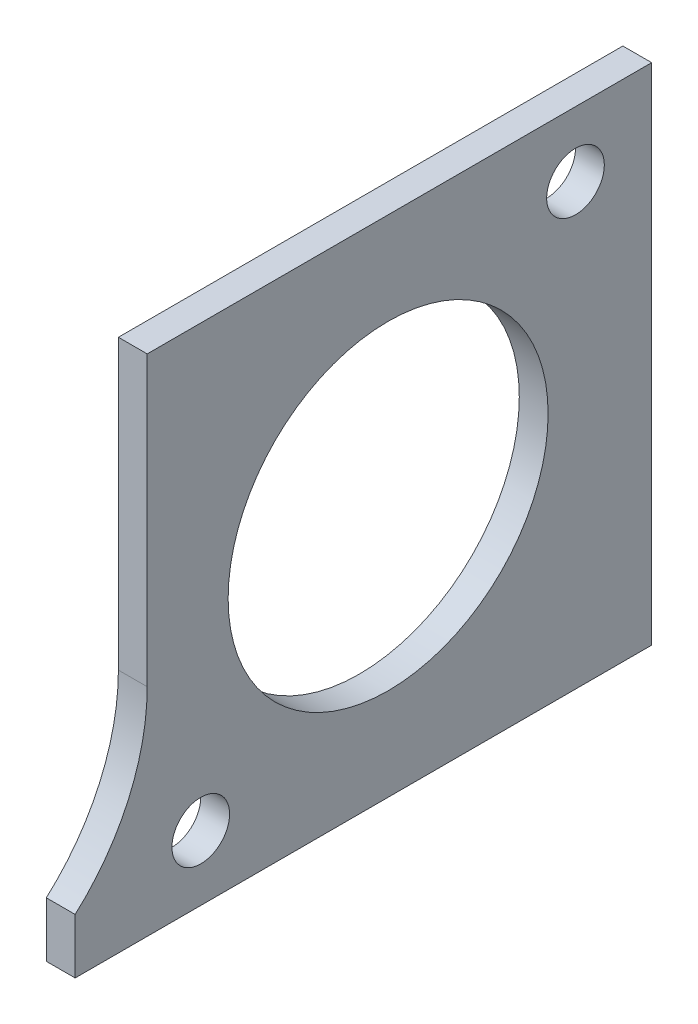
SolidWorks part; units mm, degrees
ref_plane "Front Plane" through (0, 0, 0) normal (0, 0, 1) x (1, 0, 0)
ref_plane "Top Plane" through (0, 0, 0) normal (0, 1, 0) x (1, 0, 0)
ref_plane "Right Plane" through (0, 0, 0) normal (1, 0, 0) x (0, 0, -1)
sketch "Sketch1" plane through (0, 0, 0) normal (1, 0, 0) x (0, 0, -1)
  line L1 (14.9784, -24.3431) -> (14.9784, 10.6569)
  line L2 (-20.0216, -9.3431) -> (-20.0216, 10.6569)
  line L3 (14.9784, 10.6569) -> (-20.0216, 10.6569)
  line L4 (14.9784, -24.3431) -> (-25.0216, -24.3431)
  line L5 (-25.0216, -24.3431) -> (-25.0216, -20.5235)
  arc A0 (-25.0216, -20.5235) -> (-20.0216, -9.3431) centre (-35.0216, -9.3431) ccw
  circle A2 centre (9.6929, 6.1569) radius 2
  circle A3 centre (-16.3071, -19.8431) radius 2
  circle A4 centre (-3.3071, -6.8431) radius 11.1
extrude "Boss-Extrude1" add sketch "Sketch1" along normal blind 2
